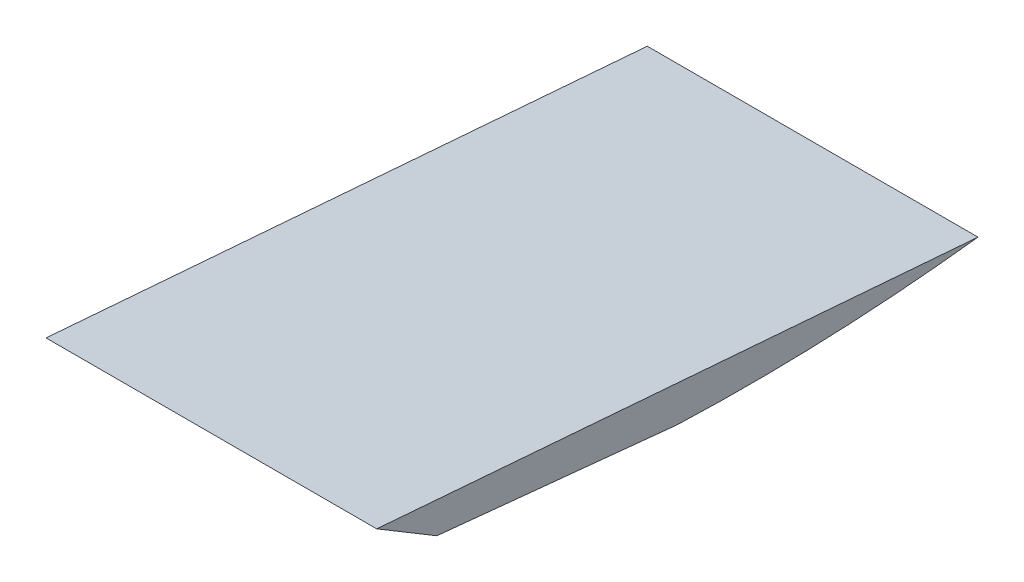
SolidWorks part; units mm, degrees
material "실리콘"
ref_plane "정면" through (0, 0, 0) normal (0, 0, 1) x (1, 0, 0)
ref_plane "윗면" through (0, 0, 0) normal (0, 1, 0) x (1, 0, 0)
ref_plane "우측면" through (0, 0, 0) normal (1, 0, 0) x (0, 0, -1)
sketch "스케치2" plane through (0, 0, 0) normal (1, 0, 0) x (0, 0, -1)
  line L0 (0, 0) -> (20, -2)
  line L2 (45, -0.9934) -> (-5, 3)
  line L3 (-5, 3) -> (0, 0)
  arc A0 (45, -0.9934) -> (20, -2) centre (26.0825, 157.8843) cw
  dimension "D5" = 160
  dimension "D1" = 50
  dimension "D2" = 20
  dimension "D3" = 3
  dimension "D4" = 2
  dimension "D6" = 3.9934
  dimension "D7" = 5
extrude "보스-돌출1" add sketch "스케치2" along normal mid plane 27.5
